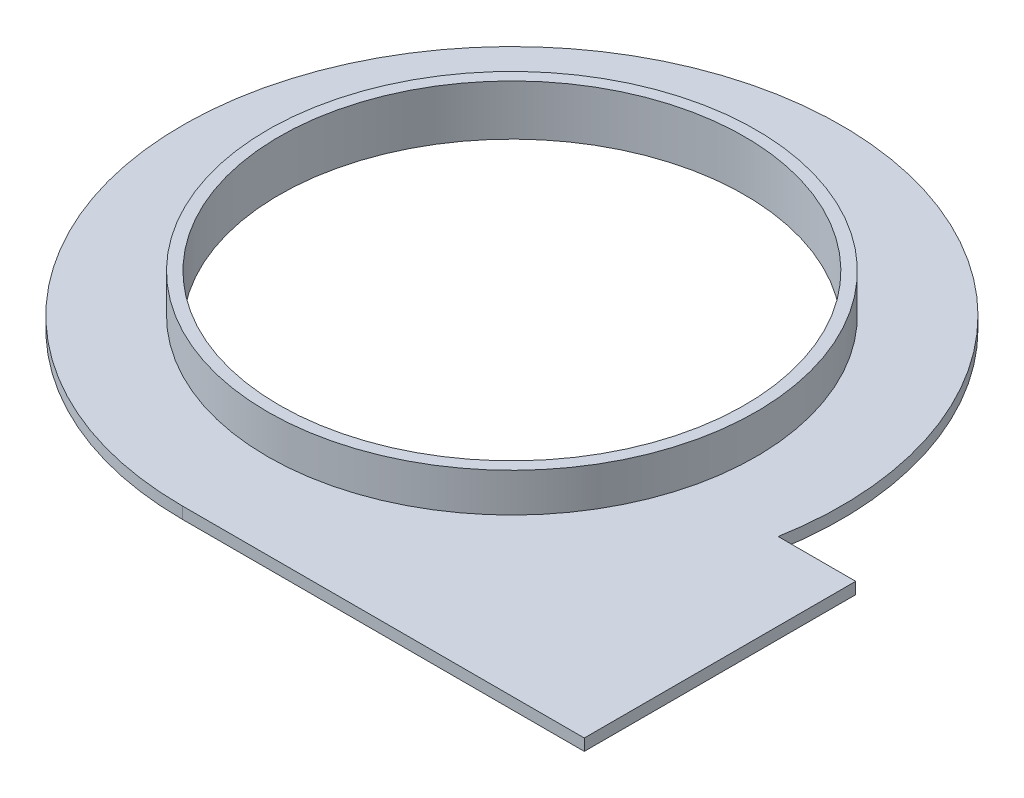
SolidWorks part; units mm, degrees
ref_plane "Front Plane" through (0, 0, 0) normal (0, 0, 1) x (1, 0, 0)
ref_plane "Top Plane" through (0, 0, 0) normal (0, 1, 0) x (1, 0, 0)
ref_plane "Right Plane" through (0, 0, 0) normal (1, 0, 0) x (0, 0, -1)
sketch "Sketch2" plane through (0, 0, 0) normal (0, 1, 0) x (1, 0, 0)
  line L1 (0, -85) -> (103.666, -85)
  line L3 (83.666, -15) -> (103.666, -15)
  line L4 (103.666, -85) -> (103.666, -15)
  arc A0 (83.666, -15) -> (0, -85) centre (0, 0) ccw
  circle A1 centre (0, 0) radius 60
  dimension "D1" = 170
  dimension "D4" = 120
  dimension "D2" = 70
  dimension "D3" = 20
extrude "Boss-Extrude1" add sketch "Sketch2" along normal blind 3
sketch "Sketch3" plane through (0, 3, 0) normal (0, 1, 0) x (1, 0, 0)
  circle A2 centre (0, 0) radius 60 construction
  circle A3 centre (0, 0) radius 60
  circle A4 centre (0, 0) radius 63
  dimension "D1" = 3
extrude "Boss-Extrude2" add sketch "Sketch3" along normal blind 10
